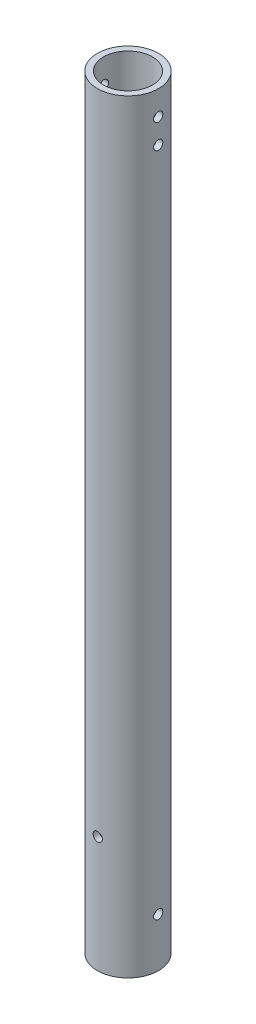
SolidWorks part; units mm, degrees
ref_plane "Front Plane" through (0, 0, 0) normal (0, 0, 1) x (1, 0, 0)
ref_plane "Top Plane" through (0, 0, 0) normal (0, 1, 0) x (1, 0, 0)
ref_plane "Right Plane" through (0, 0, 0) normal (1, 0, 0) x (0, 0, -1)
sketch "Sketch1" plane through (0, 0, 0) normal (0, 1, 0) x (1, 0, 0)
  circle A0 centre (0, 0) radius 8
  circle A1 centre (0, 0) radius 10
  dimension "D1" = 16
  dimension "D2" = 20
extrude "Boss-Extrude1" add sketch "Sketch1" along normal mid plane 250 contours A1 A0
sketch "Sketch2" plane through (0, 0, 0) normal (1, 0, 0) x (0, 0, -1)
  line L1 (10, 125) -> (-10, 125) construction
  circle A1 centre (0, 117) radius 1.5
  circle A2 centre (0, 109) radius 1.5
  point P4 (0, 0)
  dimension "D1" = 3
  dimension "D2" = 8
  dimension "D3" = 8
extrude "Cut-Extrude1" cut sketch "Sketch2" against normal up to surface and the other way up to surface up to face at (0, 125, 10) other way up to face at (0, 125, 10)
sketch "Sketch3" plane through (0, 0, 0) normal (0, 0, 1) x (1, 0, 0)
  line L1 (-10, -125) -> (10, -125) construction
  circle A2 centre (0, -87) radius 1.5
  dimension "D1" = 38
  dimension "D2" = 3
extrude "Cut-Extrude2" cut sketch "Sketch3" against normal up to surface and the other way up to surface up to face at (-9.8922, 109.3262, 1.4641) other way up to face at (-9.8922, 109.3262, 1.4641)
sketch "Sketch4" plane through (0, 0, 0) normal (1, 0, 0) x (0, 0, -1)
  line L0 (-10, -125) -> (10, -125) construction
  circle A0 centre (0, -109) radius 1.5
  dimension "D1" = 3
  dimension "42" = 16
extrude "Cut-Extrude3" cut sketch "Sketch4" against normal up to surface and the other way up to surface up to face at (-1.4641, -86.6738, -9.8922) other way up to face at (-1.4641, -86.6738, -9.8922)
